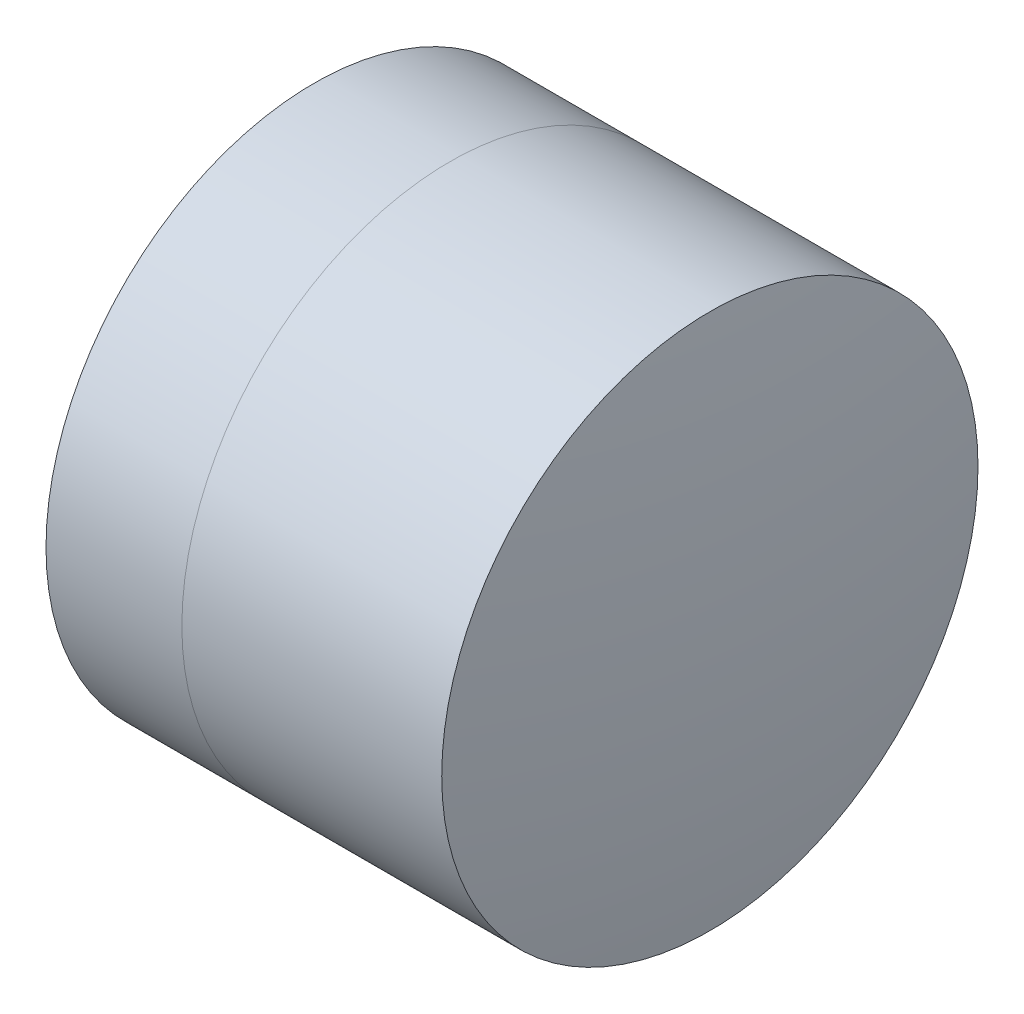
SolidWorks part; units mm, degrees
ref_plane "前视基准面" through (0, 0, 0) normal (0, 0, 1) x (1, 0, 0)
ref_plane "上视基准面" through (0, 0, 0) normal (0, 1, 0) x (1, 0, 0)
ref_plane "右视基准面" through (0, 0, 0) normal (1, 0, 0) x (0, 0, -1)
sketch "草图1" plane through (0, 0, 0) normal (0, 1, 0) x (1, 0, 0)
  line L0 (-0.8161, 0) -> (5.2377, 0) construction
  line L1 (1.9049, -2.5) -> (3.1715, -2.5)
  line L2 (1.9049, 2.5) -> (3.1715, 2.5)
  arc A0 (3.1715, -2.5) -> (3.1715, 2.5) centre (0.1782, 0) ccw
  arc A1 (1.9049, 2.5) -> (1.9049, -2.5) centre (6.5782, 0) ccw
  point P4 (5.2377, 0)
  point P10 (1.2782, 0)
  point P11 (4.0782, 0)
  dimension "D3" = 5.3
  dimension "D4" = 3.9
  dimension "D1" = 2.5
  dimension "D2" = 2.5
  dimension "D5" = 2.8
revolve "旋转1" add sketch "草图1" angle 360 about L0
sketch "草图2" plane through (0, 0, 0) normal (0, 1, 0) x (1, 0, 0)
  line L0 (-0.5519, 0) -> (6.0173, 0) construction
  line L2 (3.1715, 2.5) -> (5.5945, 2.5)
  line L3 (3.1715, -2.5) -> (5.5945, -2.5)
  arc A0 (5.5945, -2.5) -> (5.5945, 2.5) centre (-11.3218, 0) ccw
  arc A1 (3.1715, -2.5) -> (3.1715, 2.5) centre (0.1782, 0) ccw construction
  arc A2 (3.1715, -2.5) -> (3.1715, 2.5) centre (0.1782, 0) ccw
  point P4 (4.0782, 0)
  point P8 (5.7782, 0)
  point P9 (6.0173, 0)
  dimension "D1" = 17.1
  dimension "D2" = 1.7
revolve "旋转3" add sketch "草图2" angle 360 about L0
